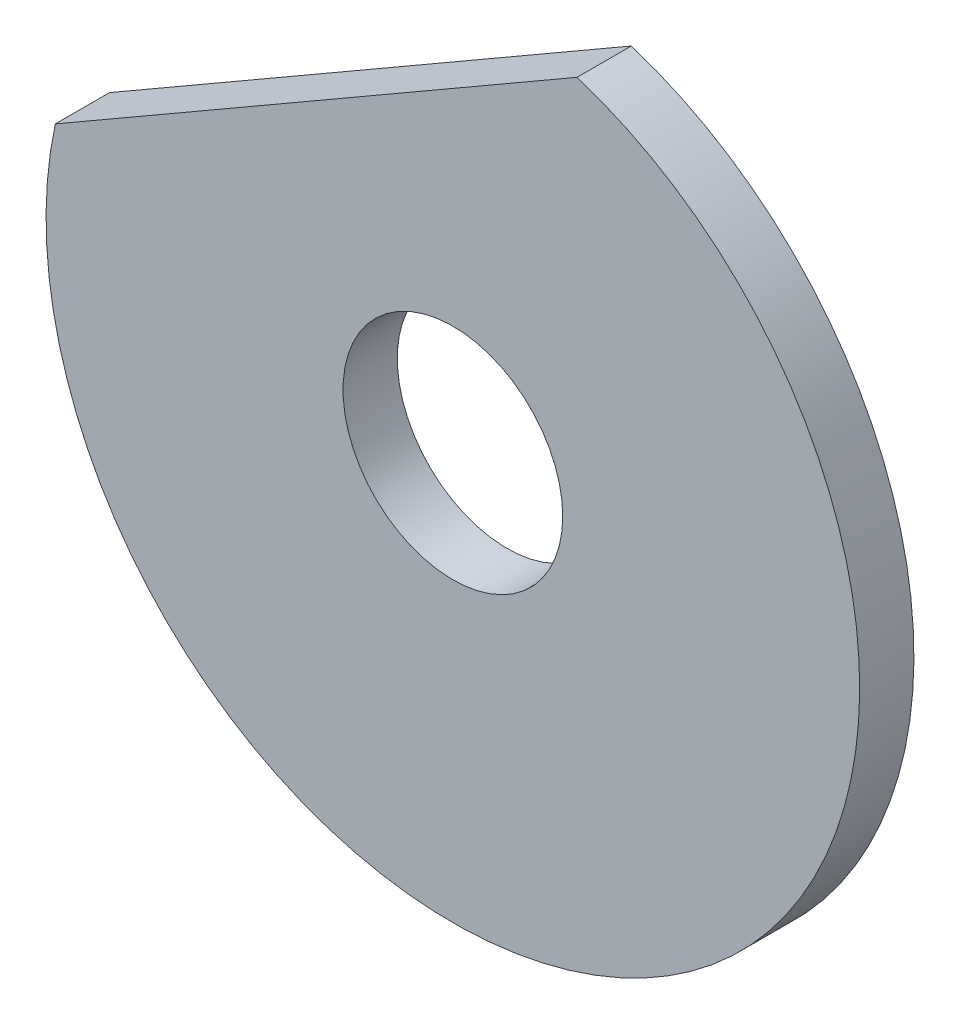
SolidWorks part; units mm, degrees
material "AISI 1020"
ref_plane "Płaszczyzna XY" through (0, 0, 0) normal (0, 0, 1) x (1, 0, 0)
ref_plane "Płaszczyzna XZ" through (0, 0, 0) normal (0, 1, 0) x (1, 0, 0)
ref_plane "Płaszczyzna YZ" through (0, 0, 0) normal (1, 0, 0) x (0, 0, -1)
sketch "Szkic1" plane through (0, 0, 0) normal (0, 0, 1) x (1, 0, 0)
  line L0 (0, -24.1072) -> (0, 24.1072) construction
  line L1 (7.5818, 7.2641) -> (9.3566, 8.2888)
  line L5 (2.5, 10.198) -> (2.5, 12.2474)
  line L8 (10.0818, 2.934) -> (11.8566, 3.9587)
  line L9 (10.0818, -2.934) -> (11.8566, -3.9587)
  line L10 (7.5818, -7.2641) -> (9.3566, -8.2888)
  line L11 (2.5, -10.198) -> (2.5, -12.2474)
  line L12 (-2.5, -10.198) -> (-2.5, -12.2474)
  line L13 (-7.5818, -7.2641) -> (-9.3566, -8.2888)
  line L14 (-10.0818, -2.934) -> (-11.8566, -3.9587)
  line L15 (-10.0818, 2.934) -> (-11.8566, 3.9587)
  line L19 (-14.6595, 3.1777) -> (4.5778, 14.2844)
  line L21 (-7.5818, 7.2641) -> (-9.3566, 8.2888) [skipped]
  arc A0 (-14.6595, 3.1777) -> (4.5778, 14.2844) centre (0, 0) ccw
  circle A1 centre (0, 0) radius 4.05
  arc A2 (-7.5818, 7.2641) -> (-2.5, 10.198) centre (0, 0) ccw
  arc A3 (-11.4406, 5.0362) -> (1.3588, 12.4259) centre (0, 0) ccw
  point P6 (0, 10.5)
  point P9 (0, 0)
  point P40 (0, 0)
  point P42 (-7.5818, 7.2641)
  dimension "D1" = 30
  dimension "D2" = 8.1
  dimension "D3" = 21
  dimension "D4" = 25
  dimension "D6" = 6
extrude "Dodanie-wyciągnięcie1" add sketch "Szkic1" along normal blind 2 contours L19 A0 | A1
sketch "Szkic3" plane through (0, 0, 0) normal (0, 0, -1) x (-1, 0, 0)
